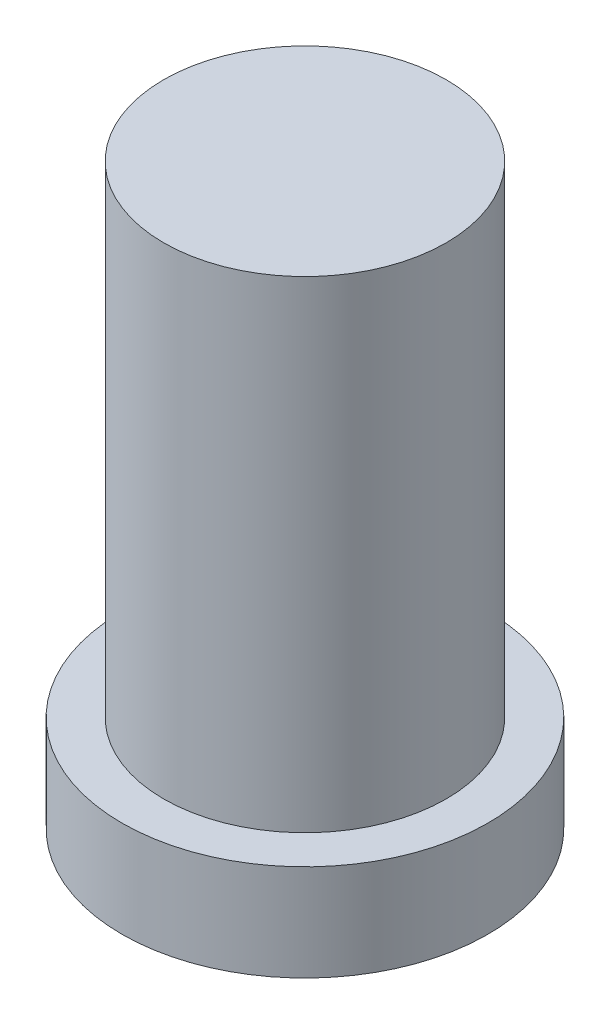
SolidWorks part; units mm, degrees
ref_plane "Front Plane" through (0, 0, 0) normal (0, 0, 1) x (1, 0, 0)
ref_plane "Top Plane" through (0, 0, 0) normal (0, 1, 0) x (1, 0, 0)
ref_plane "Right Plane" through (0, 0, 0) normal (1, 0, 0) x (0, 0, -1)
sketch "Sketch1" plane through (0, 0, 0) normal (0, 1, 0) x (1, 0, 0)
  circle A0 centre (0, 0) radius 28.5
  dimension "D1" = 57
extrude "Boss-Extrude1" add sketch "Sketch1" along normal blind 15
sketch "Sketch2" plane through (0, 15, 0) normal (0, 1, 0) x (1, 0, 0)
  circle A0 centre (0, 0) radius 22
  dimension "D1" = 44
extrude "Boss-Extrude2" add sketch "Sketch2" along normal blind 75
